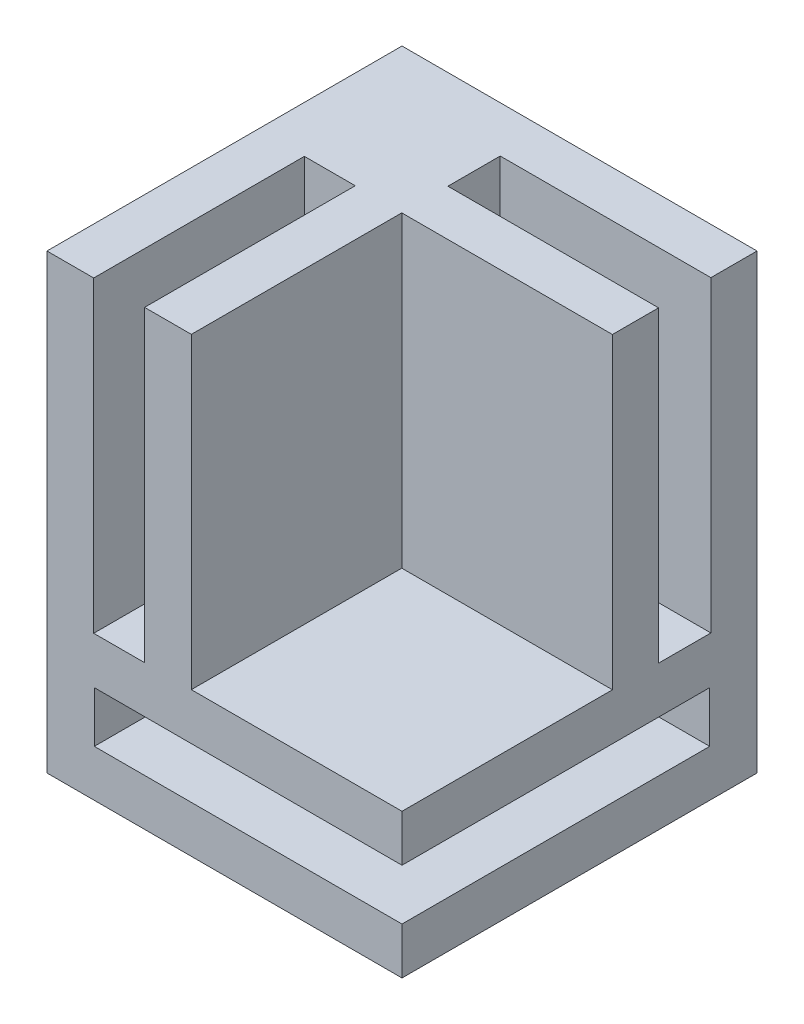
SolidWorks part; units mm, degrees
ref_plane "Plan de face" through (0, 0, 0) normal (0, 0, 1) x (1, 0, 0)
ref_plane "Plan de dessus" through (0, 0, 0) normal (0, 1, 0) x (1, 0, 0)
ref_plane "Plan de droite" through (0, 0, 0) normal (1, 0, 0) x (0, 0, -1)
sketch "Sketch1" plane through (0, 0, 0) normal (0, 0, 1) x (1, 0, 0)
  line L1 (-41.2499, 24.2978) -> (-11.2499, 24.2978)
  line L2 (-41.2499, 24.2978) -> (-41.2499, 12.0978)
  line L3 (-41.2499, 12.0978) -> (-11.2499, 12.0978)
  line L4 (-11.2499, 24.2978) -> (-11.2499, 12.0978)
  dimension "D1" = 12.2
  dimension "D2" = 30
extrude "Boss-Extrude1" add sketch "Sketch1" along normal blind 30
sketch "Sketch2" plane through (-11.2499, 0, 0) normal (1, 0, 0) x (0, 0, -1)
  line L0 (-30, 12.0978) -> (-30, 24.2978) construction
  line L1 (-30, 20.3478) -> (-4, 20.3478)
  line L2 (-30, 20.3478) -> (-30, 16.0478)
  line L3 (-30, 16.0478) -> (-4, 16.0478)
  line L4 (-4, 20.3478) -> (-4, 16.0478)
  line L5 (-30, 24.2978) -> (0, 24.2978) construction
  line L6 (-30, 12.0978) -> (0, 12.0978) construction
  line L7 (0, 12.0978) -> (0, 24.2978) construction
  dimension "D1" = 3.95
  dimension "D2" = 3.95
  dimension "D3" = 4.3
  dimension "D4" = 4
extrude "Cut-Extrude1" cut sketch "Sketch2" against normal blind 26
sketch "Sketch3" plane through (0, 24.2978, 0) normal (0, 1, 0) x (1, 0, 0)
  line L5 (-41.2499, 0) -> (-11.2499, 0)
  line L6 (-41.2499, 0) -> (-41.2499, -30)
  line L7 (-41.2499, -30) -> (-11.2499, -30)
  line L8 (-11.2499, 0) -> (-11.2499, -30)
  dimension "D1" = 30
  dimension "D2" = 30
extrude "Boss-Extrude2" add sketch "Sketch3" along normal blind 26
sketch "Sketch4" plane through (0, 50.2978, 0) normal (0, 1, 0) x (1, 0, 0)
  line L1 (-11.2499, -30) -> (-29.0499, -30)
  line L2 (-11.2499, -30) -> (-11.2499, -12.22)
  line L3 (-11.2499, -12.22) -> (-29.0499, -12.22)
  line L4 (-29.0499, -30) -> (-29.0499, -12.22)
  line L6 (-11.2499, 0) -> (-41.2499, 0) construction
  line L7 (-41.2499, 0) -> (-41.2499, -30) construction
  dimension "D1" = 12.2
  dimension "D2" = 12.22
extrude "Cut-Extrude2" cut sketch "Sketch4" against normal blind 26
sketch "Sketch6" plane through (-11.2499, 0, 0) normal (1, 0, 0) x (0, 0, -1)
  line L0 (-12.22, 50.2978) -> (0, 50.2978) construction
  line L1 (-8.32, 50.2978) -> (-3.9, 50.2978)
  line L2 (-8.32, 50.2978) -> (-8.32, 24.2978)
  line L3 (-8.32, 24.2978) -> (-3.9, 24.2978)
  line L4 (-3.9, 50.2978) -> (-3.9, 24.2978)
  line L5 (0, 12.0978) -> (0, 50.2978) construction
  line L6 (-12.22, 24.2978) -> (-12.22, 50.2978) construction
  dimension "D1" = 26
  dimension "D2" = 3.9
  dimension "D3" = 3.9
extrude "Cut-Extrude3" cut sketch "Sketch6" against normal blind 17.8
sketch "Sketch9" plane through (0, 0, 30) normal (0, 0, 1) x (1, 0, 0)
  line L0 (-41.2499, 50.2978) -> (-29.0499, 50.2978) construction
  line L1 (-37.2999, 50.2978) -> (-32.9999, 50.2978)
  line L2 (-37.2999, 50.2978) -> (-37.2999, 24.2978)
  line L3 (-37.2999, 24.2978) -> (-32.9999, 24.2978)
  line L4 (-32.9999, 50.2978) -> (-32.9999, 24.2978)
  line L5 (-41.2499, 50.2978) -> (-41.2499, 12.0978) construction
  line L6 (-29.0499, 24.2978) -> (-29.0499, 50.2978) construction
  dimension "D1" = 26
  dimension "D2" = 3.95
  dimension "D3" = 3.95
extrude "Cut-Extrude4" cut sketch "Sketch9" against normal blind 17.8
